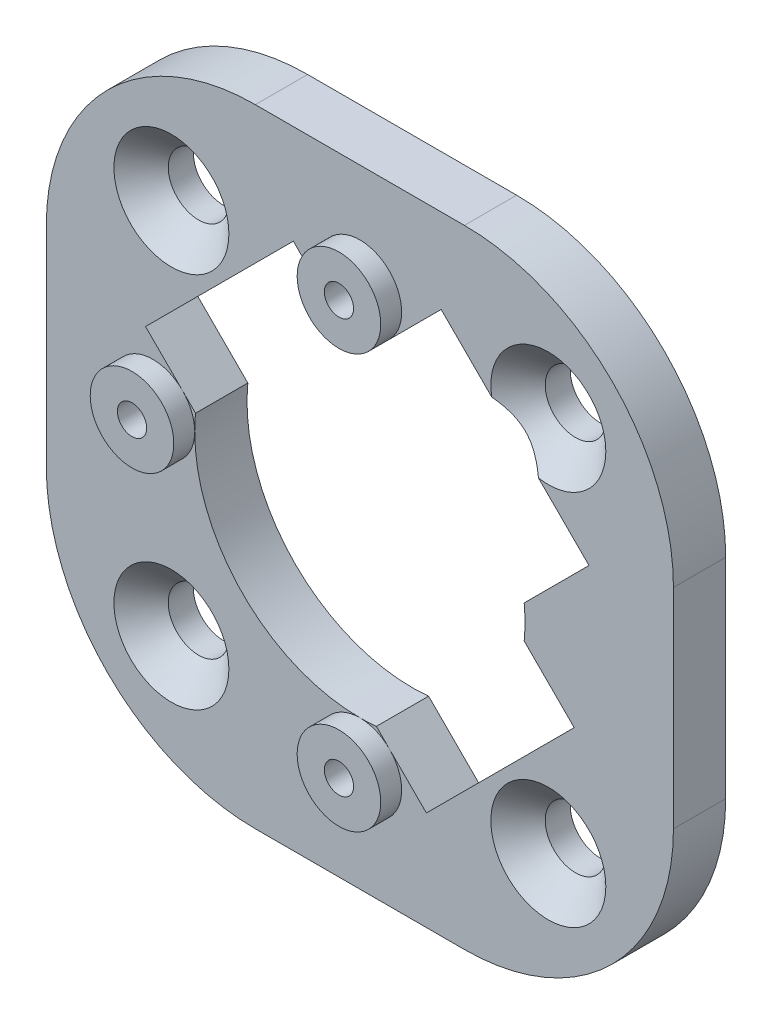
SolidWorks part; units mm, degrees
ref_plane "Front Plane" through (0, 0, 0) normal (0, 0, 1) x (1, 0, 0)
ref_plane "Top Plane" through (0, 0, 0) normal (0, 1, 0) x (1, 0, 0)
ref_plane "Right Plane" through (0, 0, 0) normal (1, 0, 0) x (0, 0, -1)
ref_plane "Plane1" through (0, 0, 0) normal (0, 0, -1) x (-1, 0, 0)
sketch "Sketch1" plane through (0, 0, 0) normal (0, 0, -1) x (-1, 0, 0)
  line L0 (15, -15) -> (15, 15)
  line L1 (15, 15) -> (-15, 15)
  line L2 (-15, 15) -> (-15, -15)
  line L3 (-15, -15) -> (15, -15)
extrude "Boss-Extrude1" add sketch "Sketch1" against normal blind 2.5
sketch "Sketch2" plane through (0, 0, 2.5) normal (0, 0, 1) x (1, 0, 0)
  line L0 (-3.182, 10.253) -> (-10.253, 3.182)
  line L1 (-10.253, 3.182) -> (-7.86, 0.7889)
  line L2 (0.7889, -7.86) -> (3.182, -10.253)
  line L3 (3.182, -10.253) -> (10.253, -3.182)
  line L4 (10.253, -3.182) -> (7.86, -0.7889)
  line L5 (7.86, 0.7889) -> (10.9602, 3.8891)
  line L6 (10.9602, 3.8891) -> (3.8891, 10.9602)
  line L7 (3.8891, 10.9602) -> (0.7889, 7.86)
  line L8 (-0.7889, 7.86) -> (-3.182, 10.253)
  arc A0 (-7.86, 0.7889) -> (0.7889, -7.86) centre (0, 0) ccw
  arc A1 (7.86, -0.7889) -> (7.86, 0.7889) centre (0, 0) ccw
  arc A2 (0.7889, 7.86) -> (-0.7889, 7.86) centre (0, 0) ccw
extrude "Cut-Extrude1" cut sketch "Sketch2" against normal through all
ref_plane "Plane2" through (0, 0, 0) normal (0, -1, 0) x (1, 0, 0)
sketch "Sketch3" plane through (0, 0, 0) normal (0, -1, 0) x (1, 0, 0)
  line L0 (-7.8995, 3.5) -> (-9.8995, 3.5)
  line L1 (-9.8995, 3.5) -> (-9.8995, 2.5)
  line L2 (-9.8995, 2.5) -> (-7.8995, 2.5)
  line L3 (-7.8995, 2.5) -> (-7.8995, 3.5)
  line L4 (-9.8995, 3.5) -> (-9.8995, 2.5) construction
revolve "Revolve1" add sketch "Sketch3" angle 360 about L4
ref_plane "Plane3" through (0, 9.8995, 0) normal (0, -1, 0) x (1, 0, 0)
sketch "Sketch4" plane through (0, 9.8995, 0) normal (0, -1, 0) x (1, 0, 0)
  line L0 (2, 3.5) -> (0, 3.5)
  line L1 (0, 3.5) -> (0, 2.5)
  line L2 (0, 2.5) -> (2, 2.5)
  line L3 (2, 2.5) -> (2, 3.5)
  line L4 (0, 3.5) -> (0, 2.5) construction
revolve "Revolve2" add sketch "Sketch4" angle 360 about L4
ref_plane "Plane4" through (0, -9.8995, 0) normal (0, -1, 0) x (1, 0, 0)
sketch "Sketch5" plane through (0, -9.8995, 0) normal (0, -1, 0) x (1, 0, 0)
  line L0 (2, 3.5) -> (0, 3.5)
  line L1 (0, 3.5) -> (0, 2.5)
  line L2 (0, 2.5) -> (2, 2.5)
  line L3 (2, 2.5) -> (2, 3.5)
  line L4 (0, 3.5) -> (0, 2.5) construction
revolve "Revolve3" add sketch "Sketch5" angle 360 about L4
hole_wizard "CSK for M2.5 Flat Head Machine Screw1" positions "Sketch7" profile "Sketch6" countersink size "M2.5" standard "ANSI Metric"
sketch "Sketch7" plane through (0, 0, 2.5) normal (0, 0, 1) x (1, 0, 0)
  point P0 (9.0156, 9.0156)
  point P1 (-9.0156, 9.0156)
  point P2 (-9.0156, -9.0156)
  point P3 (9.0156, -9.0156)
sketch "Sketch6" plane through (9.0156, 9.0156, 2.5) normal (1, 0, 0) x (0, -1, 0)
  line L0 (0, 0) -> (0, 2.5)
  line L1 (0, 2.5) -> (1.45, 2.5)
  line L2 (1.45, 2.5) -> (1.45, 1.3)
  line L3 (1.45, 1.3) -> (2.75, 0)
  line L5 (2.75, 0) -> (0, 0)
  line L6 (-1.45, 1.3) -> (-2.75, 0) construction
  line L11 (0, -6.35) -> (0, 107.95) construction
  dimension "Thru Hole Dia." = 2.9
  dimension "Thru Hole Depth" = 2.5
  dimension "Near C'Sink Dia." = 5.5
  dimension "Near C'Sink Angle" = 90
hole_wizard "Ø1.4 (1.4) Diameter Hole1" positions "Sketch9" profile "Sketch8" hole size "Ø1.4" standard "ANSI Metric"
sketch "Sketch9" plane through (0, 0, 0) normal (0, 0, -1) x (-1, 0, 0)
  point P0 (9.8995, 0)
  point P1 (0, -9.8995)
  point P2 (0, 9.8995)
sketch "Sketch8" plane through (-9.8995, 0, 0) normal (1, 0, 0) x (0, 1, 0)
  line L0 (0, 0) -> (0, 3.5)
  line L1 (0, 3.5) -> (0.7, 3.5)
  line L2 (0.7, 3.5) -> (0.7, 0)
  line L5 (0.7, 0) -> (0, 0)
  line L11 (0, -6.35) -> (0, 107.95) construction
  dimension "Thru Hole Dia." = 1.4
  dimension "Thru Hole Depth" = 3.5
fillet "Fillet1" radius 10 4 edges at (-15, 15, 1.25) (-15, -15, 1.25) (15, 15, 1.25) (15, -15, 1.25)
